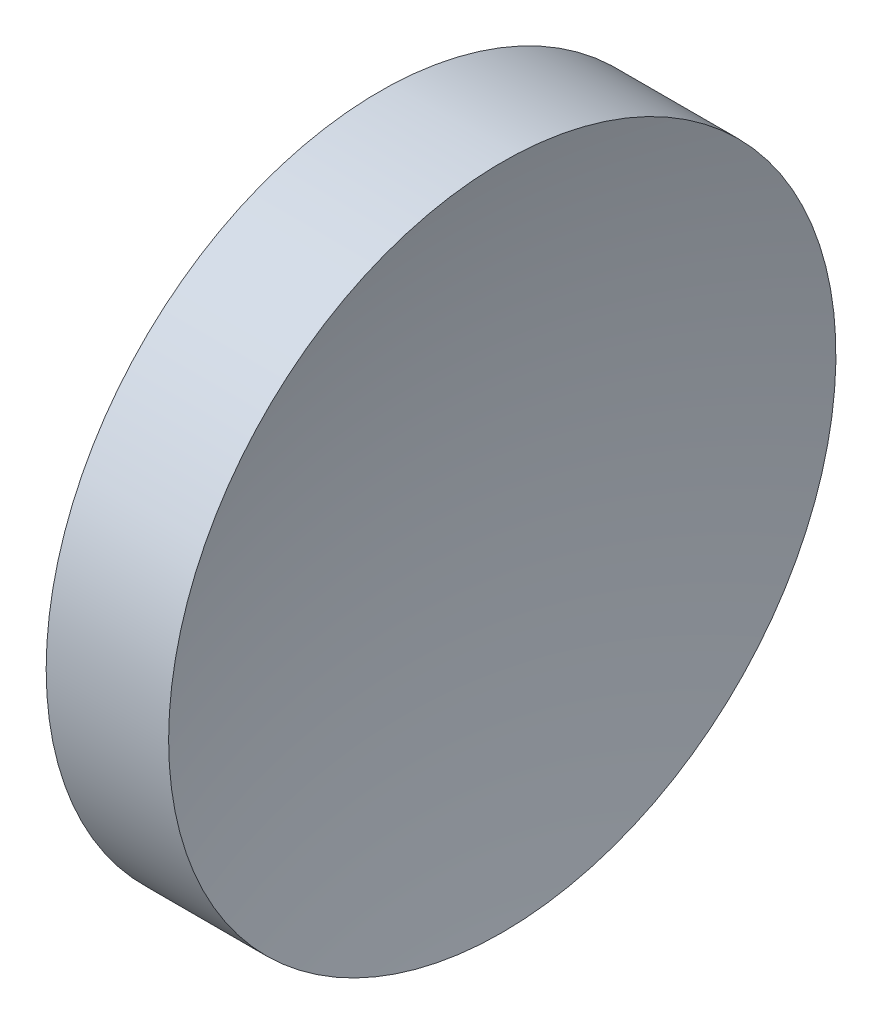
SolidWorks part; units mm, degrees
ref_plane "前视基准面" through (0, 0, 0) normal (0, 0, 1) x (1, 0, 0)
ref_plane "上视基准面" through (0, 0, 0) normal (0, 1, 0) x (1, 0, 0)
ref_plane "右视基准面" through (0, 0, 0) normal (1, 0, 0) x (0, 0, -1)
sketch "草图1" plane through (0, 0, 0) normal (0, 0, 1) x (1, 0, 0)
  line L0 (217.9703, 138.756) -> (265.5527, 138.756) construction
  line L1 (230.1996, 138.756) -> (230.1996, 176.256)
  line L2 (230.1996, 176.256) -> (243.9627, 176.256)
  line L3 (239.1996, 138.756) -> (230.1996, 138.756)
  arc A0 (243.9627, 176.256) -> (239.1996, 138.756) centre (389.1996, 138.756) ccw
  dimension "D1" = 150
revolve "旋转1" add sketch "草图1" angle 360 about L0
